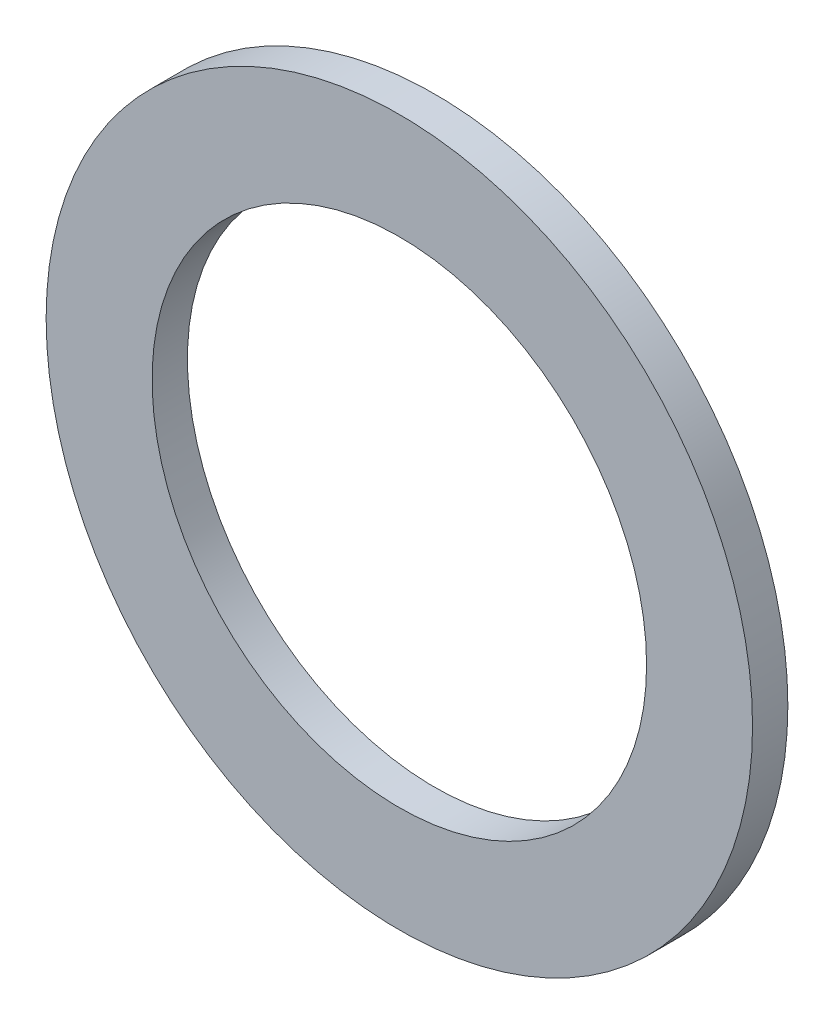
SolidWorks part; units mm, degrees
ref_plane "Front Plane" through (0, 0, 0) normal (0, 0, 1) x (1, 0, 0)
ref_plane "Top Plane" through (0, 0, 0) normal (0, 1, 0) x (1, 0, 0)
ref_plane "Right Plane" through (0, 0, 0) normal (1, 0, 0) x (0, 0, -1)
sketch "Sketch1" plane through (0, 0, 0) normal (0, 0, 1) x (1, 0, 0)
  circle A0 centre (0, 0) radius 31.75
  circle A1 centre (0, 0) radius 22.225
  dimension "D1" = 63.5
  dimension "D2" = 9.525
extrude "Boss-Extrude1" add sketch "Sketch1" along normal blind 3.175
